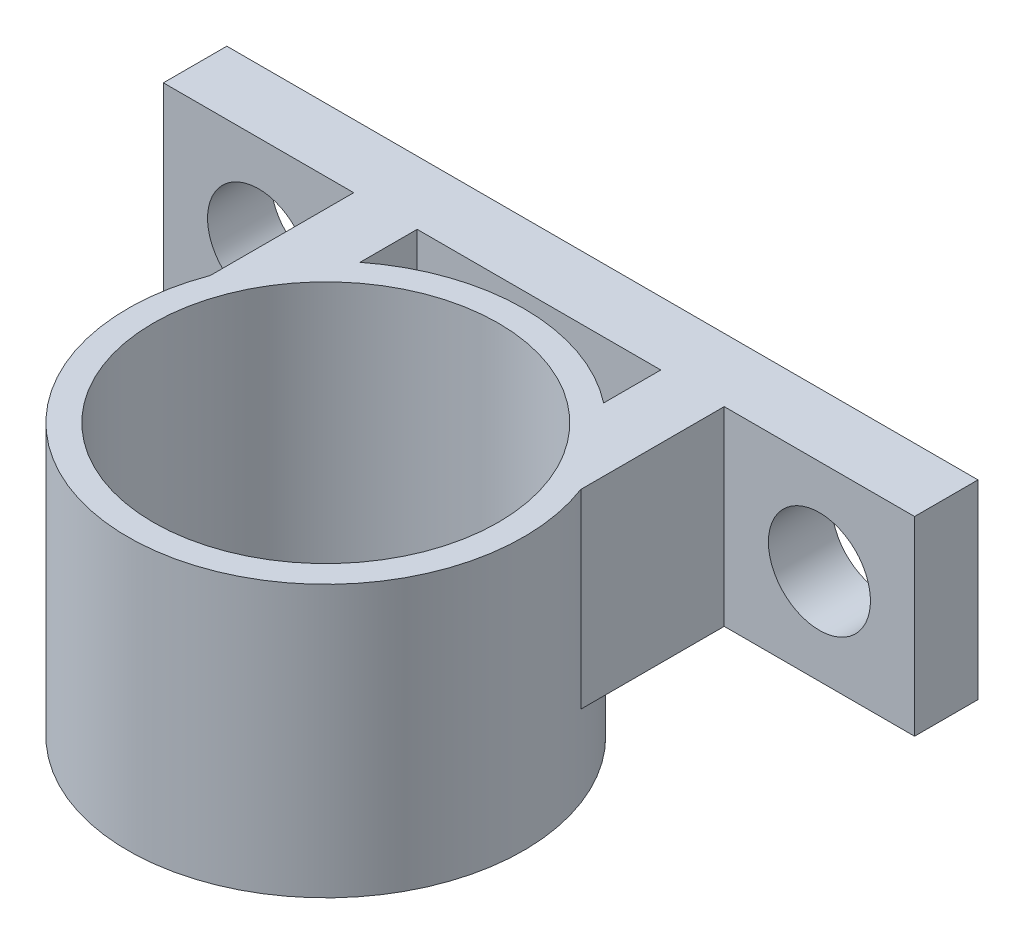
SolidWorks part; units mm, degrees
ref_plane "Front Plane" through (0, 0, 0) normal (0, 0, 1) x (1, 0, 0)
ref_plane "Top Plane" through (0, 0, 0) normal (0, 1, 0) x (1, 0, 0)
ref_plane "Right Plane" through (0, 0, 0) normal (1, 0, 0) x (0, 0, -1)
sketch "Sketch1" plane through (0, 0, 0) normal (0, 1, 0) x (1, 0, 0)
  line L0 (0, 0) -> (14.2506, 0) construction
  line L1 (0, 0) -> (0, 17.6258) construction
  line L3 (-6.096, -0.381) -> (-6.096, 13.843) construction
  line L4 (-9.271, 0) -> (-9.271, 10.668)
  line L5 (-9.271, 10.668) -> (-18.796, 10.668)
  line L6 (-6.096, 13.843) -> (-18.796, 13.843)
  line L7 (-18.796, 10.668) -> (-18.796, 13.843)
  line L9 (-6.096, 13.843) -> (6.096, 13.843)
  line L11 (9.271, 0) -> (9.271, 10.668)
  line L12 (18.796, 10.668) -> (18.796, 13.843)
  line L13 (6.096, 13.843) -> (18.796, 13.843)
  line L14 (9.271, 10.668) -> (18.796, 10.668)
  line L17 (-6.096, 6.731) -> (-6.096, 10.668)
  line L18 (6.096, 6.731) -> (6.096, 10.668)
  line L19 (-6.096, 10.668) -> (6.096, 10.668)
  circle A0 centre (0, 0) radius 6.096
  circle A1 centre (0, 0) radius 9.271 construction
  arc A3 (9.271, 0) -> (-9.271, 0) centre (0, 0) cw
  arc A5 (-6.096, 6.731) -> (6.096, 6.731) centre (0, 0) cw
  point P18 (0, 13.843)
  point P19 (0, 10.668)
  dimension "D1" = 12.192
  dimension "D2" = 3.175
  dimension "D3" = 14.224
  dimension "D4" = 3.175
  dimension "D5" = 12.7
extrude "Boss-Extrude1" add sketch "Sketch1" along normal blind 9.525
sketch "Sketch2" plane through (0, 0, -10.668) normal (0, 0, 1) x (1, 0, 0)
  line L0 (-18.796, 4.7625) -> (-9.271, 4.7625) construction
  line L1 (-18.796, 9.525) -> (-18.796, 0) construction
  line L2 (-9.271, 9.525) -> (-9.271, 0) construction
  line L3 (-14.0335, 9.525) -> (-14.0335, 0) construction
  line L4 (-18.796, 9.525) -> (-9.271, 9.525) construction
  line L5 (-18.796, 0) -> (-9.271, 0) construction
  line L6 (0, 0) -> (0, 9.525) construction
  line L7 (9.271, 9.525) -> (-9.271, 9.525) construction
  circle A0 centre (-14.0335, 4.7625) radius 2.5527
  circle A1 centre (14.0335, 4.7625) radius 2.5527
  dimension "D1" = 5.1054
extrude "Cut-Extrude1" cut sketch "Sketch2" against normal through all
sketch "Sketch3" plane through (0, 0, 0) normal (0, -1, 0) x (-1, 0, 0)
  circle A0 centre (0, 0) radius 6.096
  circle A3 centre (0, 0) radius 9.271
  arc A4 (-9.271, 0) -> (9.271, 0) centre (0, 0) ccw construction
  circle A5 centre (0, 0) radius 6.096 construction
  dimension "D1" = 0
  dimension "D2" = 0
extrude "Boss-Extrude2" add sketch "Sketch3" along normal blind 2.794
sketch "Sketch6" plane through (0, 9.525, 0) normal (0, 1, 0) x (1, 0, 0)
  circle A0 centre (0, 0) radius 8.636
  circle A1 centre (0, 0) radius 9.906
  dimension "D1" = 1.27
extrude "Boss-Extrude4" add sketch "Sketch6" against normal up to surface (12.319 mm away) up to face at (0, -2.794, -9.271)
sketch "Sketch5" plane through (0, 9.525, 0) normal (0, 1, 0) x (1, 0, 0)
  circle A0 centre (0, 0) radius 8.636
  dimension "D1" = 17.272
extrude "Cut-Extrude2" cut sketch "Sketch5" against normal up to surface (12.319 mm away)
sketch "Sketch4" plane through (0, -2.794, 0) normal (0, -1, 0) x (-1, 0, 0)
  circle A2 centre (0, 0) radius 9.906
  circle A3 centre (0, 0) radius 7.366
  circle A4 centre (0, 0) radius 9.906 construction
  dimension "D1" = 0
  dimension "D2" = 14.732
extrude "Boss-Extrude3" add sketch "Sketch4" along normal blind 1.27 contours A2 | A3
